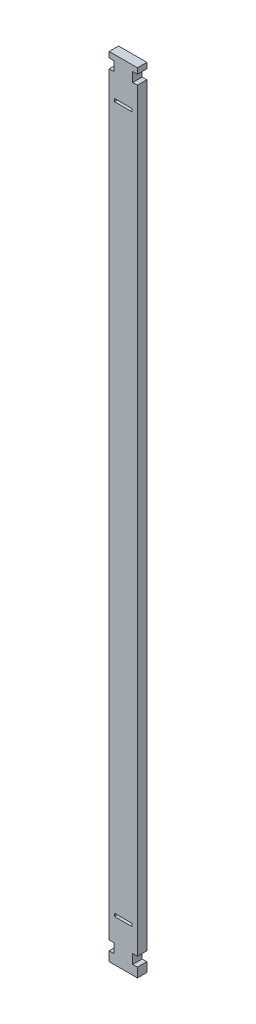
SolidWorks part; units mm, degrees
ref_plane "前视基准面" through (0, 0, 0) normal (0, 0, 1) x (1, 0, 0)
ref_plane "上视基准面" through (0, 0, 0) normal (0, 1, 0) x (1, 0, 0)
ref_plane "右视基准面" through (0, 0, 0) normal (1, 0, 0) x (0, 0, -1)
sketch "草图1" plane through (0, 0, 0) normal (0, 0, 1) x (1, 0, 0)
  line L1 (-7.5, -225) -> (7.5, -225)
  line L2 (-7.5, -225) -> (-7.5, 225)
  line L3 (-7.5, 225) -> (7.5, 225)
  line L4 (7.5, -225) -> (7.5, 225)
  line L5 (-7.5, -225) -> (7.5, 225) construction
  line L6 (-7.5, 225) -> (7.5, -225) construction
  point P0 (0, 0)
  dimension "D1" = 450
  dimension "D2" = 15
extrude "凸台-拉伸1" add sketch "草图1" along normal blind 5
sketch "草图2" plane through (0, 0, 5) normal (0, 0, 1) x (1, 0, 0)
  line L0 (-7.5, 225) -> (-7.5, -225) construction
  line L1 (-7.5, -215) -> (-5, -215)
  line L2 (-7.5, -215) -> (-7.5, -220)
  line L3 (-7.5, -220) -> (-5, -220)
  line L4 (-5, -215) -> (-5, -220)
  line L5 (-7.5, -215) -> (-5, -220) construction
  line L6 (-7.5, -220) -> (-5, -215) construction
  line L7 (7.5, -225) -> (7.5, 225) construction
  line L8 (7.5, -215) -> (5, -215)
  line L9 (7.5, -215) -> (7.5, -220)
  line L10 (7.5, -220) -> (5, -220)
  line L11 (5, -215) -> (5, -220)
  line L12 (7.5, -215) -> (5, -220) construction
  line L13 (7.5, -220) -> (5, -215) construction
  line L14 (-7.5, -225) -> (7.5, -225) construction
  line L16 (-7.5, 190) -> (-5, 190)
  line L17 (-7.5, 190) -> (-7.5, 185)
  line L18 (-7.5, 185) -> (-5, 185)
  line L19 (-5, 190) -> (-5, 185)
  line L20 (-7.5, 190) -> (-5, 185) construction
  line L21 (-7.5, 185) -> (-5, 190) construction
  line L22 (7.5, 190) -> (5, 190)
  line L23 (7.5, 190) -> (7.5, 185)
  line L24 (7.5, 185) -> (5, 185)
  line L25 (5, 190) -> (5, 185)
  line L26 (7.5, 190) -> (5, 185) construction
  line L27 (7.5, 185) -> (5, 190) construction
  line L28 (-7.5, 225) -> (7.5, 225)
  line L29 (-7.5, 225) -> (-7.5, 193)
  line L30 (-7.5, 193) -> (7.5, 193)
  line L31 (7.5, 225) -> (7.5, 193)
  line L32 (-7.5, 225) -> (7.5, 193) construction
  line L33 (-7.5, 193) -> (7.5, 225) construction
  point P4 (-6.25, -217.5)
  point P11 (6.25, -217.5)
  point P20 (-6.25, 187.5)
  point P25 (6.25, 187.5)
  point P30 (0, 209)
  dimension "D1" = 2.5
  dimension "D2" = 2.5
  dimension "D3" = 5
  dimension "D4" = 5
  dimension "D5" = 5
  dimension "D6" = 5
  dimension "D7" = 400
  dimension "D8" = 400
  dimension "D9" = 5
  dimension "D10" = 5
  dimension "D11" = 2.5
  dimension "D12" = 2.5
  dimension "D13" = 3
extrude "切除-拉伸1" cut sketch "草图2" against normal up to next
sketch "草图3" plane through (0, 0, 5) normal (0, 0, 1) x (1, 0, 0)
  line L0 (-5, -215) -> (-7.5, -215) construction
  line L1 (-4.75, -201.335) -> (4.75, -201.335)
  line L2 (-4.75, -201.335) -> (-4.75, -202.835)
  line L3 (-4.75, -202.835) -> (4.75, -202.835)
  line L4 (4.75, -201.335) -> (4.75, -202.835)
  line L5 (-4.75, -201.335) -> (4.75, -202.835) construction
  line L6 (-4.75, -202.835) -> (4.75, -201.335) construction
  line L8 (-4.75, 171.335) -> (4.75, 171.335)
  line L9 (-4.75, 171.335) -> (-4.75, 172.835)
  line L10 (-4.75, 172.835) -> (4.75, 172.835)
  line L11 (4.75, 171.335) -> (4.75, 172.835)
  line L12 (-4.75, 171.335) -> (4.75, 172.835) construction
  line L13 (-4.75, 172.835) -> (4.75, 171.335) construction
  point P0 (0, -202.085)
  point P9 (0, 172.085)
  dimension "D1" = 9.5
  dimension "D2" = 1.5
  dimension "D3" = 13.665
  dimension "D4" = 1.5
  dimension "D5" = 13.665
  dimension "D6" = 9.5
extrude "切除-拉伸2" cut sketch "草图3" against normal up to next
